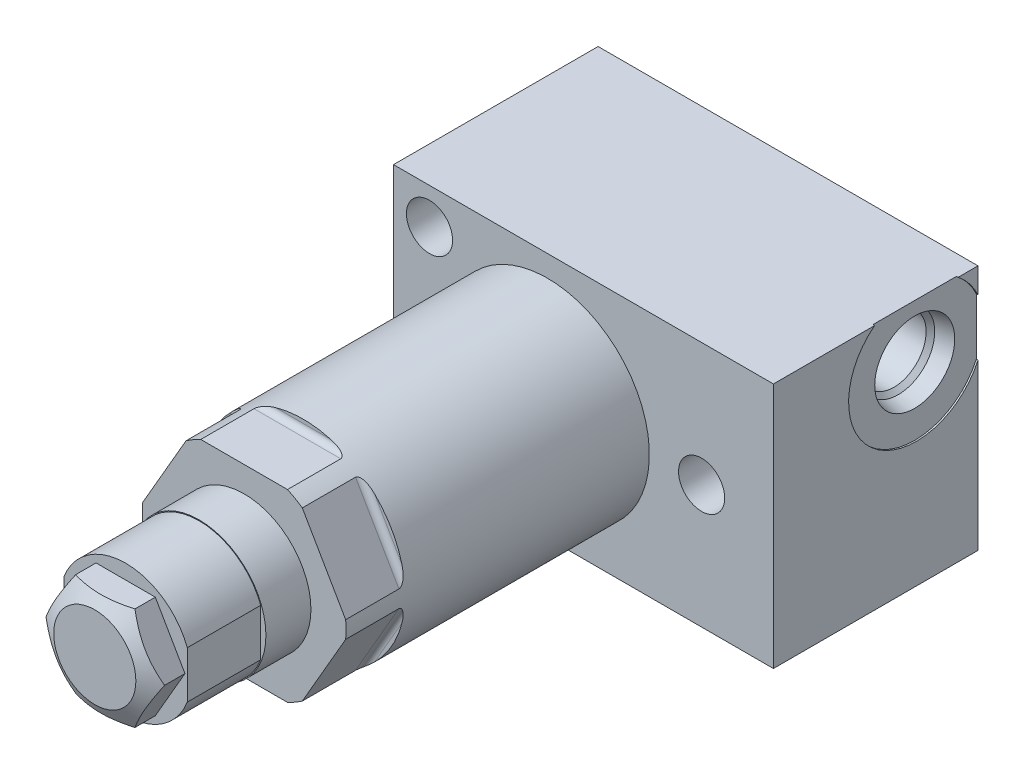
SolidWorks part; units mm, degrees
material "Alloy Steel"
ref_plane "Front" through (0, 0, 0) normal (0, 0, 1) x (1, 0, 0)
ref_plane "Top" through (0, 0, 0) normal (0, 1, 0) x (1, 0, 0)
ref_plane "Right" through (0, 0, 0) normal (1, 0, 0) x (0, 0, -1)
ref_plane "Plane1" through (0, 0, 0) normal (0, 0, 1) x (1, 0, 0)
ref_plane "Plane2" through (0, 0, 0) normal (0, 0, 1) x (1, 0, 0)
sketch "Sketch1" plane through (0, 0, 0) normal (0, 0, 1) x (1, 0, 0)
  circle A0 centre (0, 0) radius 15.748
  dimension "D1" = 31.496
extrude "Extrude1" add sketch "Sketch1" along normal blind 67.8434
ref_plane "Plane3" through (0, 0, 0) normal (1, 0, 0) x (0, 0, 1)
sketch "Sketch2" plane through (0, 0, 0) normal (1, 0, 0) x (0, 0, 1)
  line L0 (58.6994, 15.748) -> (58.6994, 15.1638)
  line L1 (59.6138, 14.2494) -> (67.8434, 14.2494)
  line L2 (45.6692, 0) -> (55.7276, 0) construction
  line L3 (67.8434, -15.748) -> (67.8434, 15.748) construction
  line L4 (58.6994, 15.748) -> (67.8434, 15.748)
  line L5 (67.8434, 15.748) -> (67.8434, 14.2494)
  arc A0 (58.6994, 15.1638) -> (59.6138, 14.2494) centre (59.6138, 15.1638) ccw
  dimension "D2" = 0.9144
  dimension "D1" = 28.4988
  dimension "D3" = 9.144
extrude "Cut-Extrude1" cut sketch "Sketch2" against normal mid plane 37.7952
ref_plane "Plane13" through (0, 0, 0) normal (1, 0, 0) x (0, 0, 1)
sketch "Sketch10" plane through (0, 0, 0) normal (1, 0, 0) x (0, 0, 1)
  line L0 (0, 14.8717) -> (7.7978, 14.8717)
  line L1 (7.7978, 14.8717) -> (8.6741, 15.748)
  line L2 (8.6741, 15.748) -> (0, 15.748)
  line L3 (0, 15.748) -> (0, 14.8717)
  line L4 (-0.4337, 0) -> (9.1078, 0) construction
  line L5 (58.6994, 15.748) -> (0, 15.748) construction
  line L6 (0, 15.748) -> (0, -15.748) construction
  dimension "D1" = 29.7434
  dimension "D2" = 45
  dimension "D3" = 7.7978
revolve "Cut-Revolve1" cut sketch "Sketch10" angle 360 about L4
ref_plane "Plane14" through (0, 0, 0) normal (1, 0, 0) x (0, 0, -1)
sketch "Sketch11" plane through (0, 0, 0) normal (1, 0, 0) x (0, 0, -1)
  line L0 (-67.8434, 0) -> (-86.1568, 0)
  line L1 (-86.1568, 0) -> (-86.1568, 10.3251)
  line L2 (-86.1568, 10.3251) -> (-67.8434, 10.3251)
  line L3 (-67.8434, 10.3251) -> (-67.8434, 0)
  line L4 (-71.1543, 0) -> (-36.7188, 0) construction
  line L5 (-67.8434, 15.748) -> (-67.8434, -14.2494) construction
  dimension "D1" = 20.6502
  dimension "D2" = 18.3134
revolve "Revolve1" add sketch "Sketch11" angle 360 about L4
ref_plane "Plane17" through (0, 0, 59.055) normal (0, 0, -1) x (0, 1, 0)
sketch "Sketch14" plane through (0, 0, 86.1568) normal (0, 0, -1) x (0, 1, 0)
  line L0 (-3.9852, 9.525) -> (3.9852, 9.525)
  line L1 (-3.9852, -9.525) -> (3.9852, -9.525)
  line L2 (-11.3576, 0) -> (11.3576, 0) construction
  arc A0 (3.9852, 9.525) -> (-3.9852, 9.525) centre (0, 0) ccw
  arc A1 (-3.9852, -9.525) -> (3.9852, -9.525) centre (0, 0) ccw
  dimension "D2" = 10.3251
  dimension "D1" = 19.05
extrude "Cut-Extrude10" cut sketch "Sketch14" along normal blind 11.3538
sketch "Sketch15" plane through (0, 0, 86.1568) normal (0, 0, 1) x (1, 0, 0)
  line L0 (-4.5827, 7.9375) -> (4.5827, 7.9375)
  line L1 (4.5827, 7.9375) -> (9.1654, 0)
  line L2 (9.1654, 0) -> (4.5827, -7.9375)
  line L3 (4.5827, -7.9375) -> (-4.5827, -7.9375)
  line L4 (-4.5827, -7.9375) -> (-9.1654, 0)
  line L5 (-9.1654, 0) -> (-4.5827, 7.9375)
  line L6 (-10.082, 0) -> (10.082, 0) construction
  dimension "D1" = 15.875
extrude "Extrude2" add sketch "Sketch15" along normal blind 4.7752
ref_plane "Plane18" through (0, 0, 0) normal (0, 1, 0) x (1, 0, 0)
sketch "Sketch16" plane through (0, 0, 0) normal (0, 1, 0) x (1, 0, 0)
  line L0 (6.35, -90.932) -> (9.1654, -89.3065)
  line L1 (0, -75.2653) -> (0, -73.4772) construction
  line L2 (9.1654, -89.3065) -> (9.1654, -90.932)
  line L3 (9.1654, -90.932) -> (6.35, -90.932)
  dimension "D1" = 30
  dimension "D2" = 12.7
revolve "Cut-Revolve3" cut sketch "Sketch16" angle 360 about L1
ref_plane "Plane19" through (0, 0, 0) normal (0, 1, 0) x (-1, 0, 0)
sketch "Sketch17" plane through (0, 0, 0) normal (0, 1, 0) x (-1, 0, 0)
  line L0 (-34.925, -10.668) -> (23.7998, -10.668)
  line L1 (23.7998, -10.668) -> (23.7998, 20.955)
  line L2 (23.7998, 20.955) -> (-34.925, 20.955)
  line L3 (-34.925, 20.955) -> (-34.925, -10.668)
  line L4 (-14.8717, 0) -> (14.8717, 0) construction
  dimension "D1" = 10.668
  dimension "D2" = 31.623
  dimension "D3" = 58.7248
  dimension "D4" = 23.7998
extrude "Extrude4" add sketch "Sketch17" along normal mid plane 38.1
ref_plane "Plane21" through (34.925, -19.05, 0) normal (1, 0, 0) x (0, 1, 0)
sketch "Sketch19" plane through (34.925, -19.05, 0) normal (1, 0, 0) x (0, 1, 0)
  line L0 (38.1, -10.668) -> (0, -10.668) construction
  circle A0 centre (29.845, -1.143) radius 10.4775
  dimension "D1" = 20.955
  dimension "D2" = 9.525
  dimension "D3" = 10.795
extrude "Cut-Extrude12" cut sketch "Sketch19" against normal blind 0.254
ref_plane "Plane22" through (34.671, 10.795, -1.143) normal (0, 0, 1) x (0, -1, 0)
sketch "S2D0001" plane through (34.671, 10.795, -1.143) normal (0, 0, 1) x (0, -1, 0)
  line L0 (0, 0) -> (6.1849, 0)
  line L1 (6.1849, 0) -> (5.6423, -2.5527)
  line L2 (5.6423, -2.5527) -> (4.9784, -3.2166)
  line L3 (4.9784, -3.2166) -> (4.9784, -17.272)
  line L4 (4.9784, -17.272) -> (0, -17.272)
  line L5 (0, -17.272) -> (0, 0)
  line L6 (0, -18.1356) -> (0, 0.8636) construction
  dimension "D1" = 17.272
revolve "Cut-Revolve4" cut sketch "S2D0001" angle 360 about L6
ref_plane "Plane23" through (0, 0, -9.3293) normal (0, 1, 0) x (-1, 0, 0)
sketch "Sketch21" plane through (0, 0, -9.3293) normal (0, 1, 0) x (-1, 0, 0)
  line L0 (0, -1.3387) -> (7.9375, -1.3387)
  line L1 (7.9375, -1.3387) -> (7.9375, 1.3283)
  line L2 (7.9375, 1.3283) -> (3.4544, 1.3283)
  line L3 (3.4544, 1.3283) -> (3.4544, 13.3933)
  line L4 (3.4544, 13.3933) -> (0, 15.4689)
  line L5 (0, 15.4689) -> (0, -1.3387)
  line L6 (0, -2.1791) -> (0, 16.3093) construction
revolve "Cut-Revolve5" cut sketch "Sketch21" angle 360 about L6
ref_plane "Plane24" through (0, 0, -9.3293) normal (0, 1, 0) x (-1, 0, 0)
sketch "Sketch22" plane through (0, 0, -9.3293) normal (0, 1, 0) x (-1, 0, 0)
  line L0 (0, -1.472) -> (0, 1.4617) construction
  circle A0 centre (-6.604, -0.0052) radius 1.3335
revolve "Revolve2" add sketch "Sketch22" angle 360 about L0
pattern_circular "CirPattern2" count 6 over 360 about axis through (0, 0, 0) along (0, 0, 1) of "Cut-Extrude1"
hole_wizard "Hole1" positions "Sketch24" profile "Sketch23" legacy end condition up to next
sketch "Sketch24" plane through (0, 0, 20.955) normal (0, 0, 1) x (1, 0, 0)
  line L0 (0, 0) -> (26.6789, 0) construction
  point P0 (-18.2626, -13.4874)
  point P6 (23.8252, 0)
  point P10 (-18.2372, 13.4874)
  dimension "D1" = 23.8252
  dimension "D2" = 13.4874
  dimension "D3" = 18.2626
  dimension "D4" = 18.2372
  dimension "D5" = 26.9748
sketch "Sketch23" plane through (-18.2626, -13.4874, 20.955) normal (1, 0, 0) x (0, -1, 0)
  line L0 (0, 0) -> (0, 31.623)
  line L1 (0, 31.623) -> (3.5687, 31.623)
  line L2 (3.5687, 31.623) -> (3.5687, 0)
  line L3 (3.5687, 0) -> (0, 0)
  line L4 (0, 110) -> (0, -10) construction
  dimension "Diameter" = 7.1374
  dimension "Depth" = 31.623
sketch "Sketch25" plane through (0, 0, 0) normal (1, 0, 0) x (0, 0, -1)
  line L0 (10.7079, 0) -> (-90.932, 0) construction
  line L1 (50, 0) -> (-50, 0) construction
  line L2 (-90.932, 6.35) -> (-90.932, -6.35) construction
  line L3 (-86.1568, 10.1981) -> (-74.803, 10.1981)
  line L4 (-86.1568, 10.3251) -> (-86.1568, 3.9852) construction
  line L5 (-74.803, 10.1981) -> (-74.803, 10.3251)
  line L6 (-67.8434, 10.3251) -> (-86.1568, 10.3251) construction
  line L7 (-74.803, 10.3251) -> (-86.1568, 10.3251)
  line L8 (-86.1568, 10.3251) -> (-86.1568, 10.1981)
  dimension "D1" = 11.3538
  dimension "D2" = 20.3962
revolve "Cut-Revolve6" cut sketch "Sketch25" angle 360 about L0
